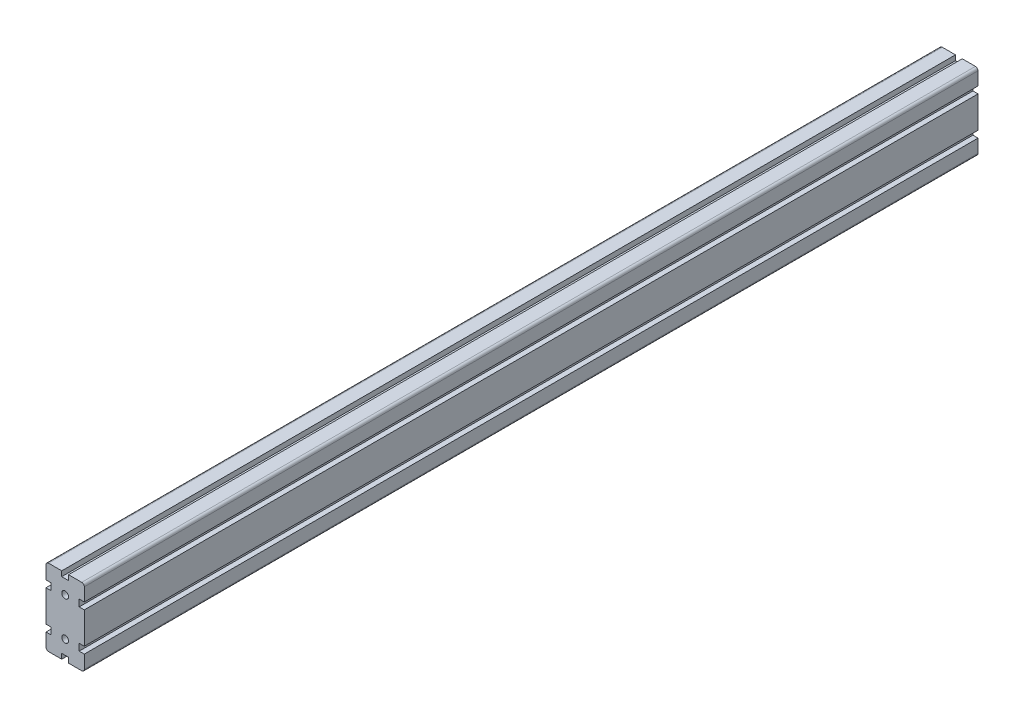
SolidWorks part; units mm, degrees
material "Zinc AC41A Alloy, As Cast"
ref_plane "Plan de face" through (0, 0, 0) normal (0, 0, 1) x (1, 0, 0)
ref_plane "Plan de dessus" through (0, 0, 0) normal (0, 1, 0) x (1, 0, 0)
ref_plane "Plan de droite" through (0, 0, 0) normal (1, 0, 0) x (0, 0, -1)
ref_plane "Plan1" through (0, 0, -1000) normal (0, 0, -1) x (-1, 0, 0)
sketch "Esquisse1" plane through (0, 0, -1000) normal (0, 0, -1) x (-1, 0, 0)
  line L0 (16.5, 26.5) -> (22.5, 26.5)
  line L1 (22.5, 26.5) -> (22.5, 42)
  line L2 (19.5, 45) -> (4, 45)
  line L3 (4, 45) -> (4, 39)
  line L4 (0, 22.5) -> (0, -22.5) construction
  line L5 (0, 22.5) -> (13.1479, 22.5) construction
  line L6 (0, -22.5) -> (12.9679, -22.5) construction
  line L7 (-4, 39) -> (-4, 45)
  line L8 (-4, 45) -> (-19.5, 45)
  line L9 (-22.5, 42) -> (-22.5, 26.5)
  line L10 (-22.5, 26.5) -> (-16.5, 26.5)
  line L11 (-16.5, 18.5) -> (-22.5, 18.5)
  line L12 (-22.5, 18.5) -> (-22.5, -18.5)
  line L13 (-4, -39) -> (4, -39)
  line L14 (16.5, -18.5) -> (16.5, -26.5)
  line L15 (-16.5, -18.5) -> (-16.5, -26.5)
  line L16 (16.5, 26.5) -> (16.5, 18.5)
  line L17 (-22.5, -18.5) -> (-16.5, -18.5)
  line L18 (-16.5, -26.5) -> (-22.5, -26.5)
  line L19 (-22.5, -26.5) -> (-22.5, -42)
  line L20 (-19.5, -45) -> (-4, -45)
  line L21 (-4, -45) -> (-4, -39)
  line L22 (4, -39) -> (4, -45)
  line L23 (4, -45) -> (19.5, -45)
  line L24 (22.5, -42) -> (22.5, -26.5)
  line L25 (22.5, -26.5) -> (16.5, -26.5)
  line L26 (16.5, -18.5) -> (22.5, -18.5)
  line L27 (-16.5, 26.5) -> (-16.5, 18.5)
  line L28 (-4, 39) -> (4, 39)
  line L29 (22.5, -18.5) -> (22.5, 18.5)
  line L30 (22.5, 18.5) -> (16.5, 18.5)
  arc A0 (22.5, 42) -> (19.5, 45) centre (19.5, 42) ccw
  arc A1 (-19.5, 45) -> (-22.5, 42) centre (-19.5, 42) ccw
  arc A2 (-22.5, -42) -> (-19.5, -45) centre (-19.5, -42) ccw
  arc A3 (19.5, -45) -> (22.5, -42) centre (19.5, -42) ccw
  circle A4 centre (0, 22.5) radius 4
  circle A5 centre (0, -22.5) radius 4
  dimension "D3" = 8
  dimension "D4" = 8
  dimension "D1" = 4
  dimension "D2" = 4
  dimension "D5" = 45
  dimension "D6" = 22.5
  dimension "D7" = 22.5
  dimension "D8" = 22.5
  dimension "D9" = 90
  dimension "D10" = 45
extrude "Boss.-Extru.1" add sketch "Esquisse1" against normal blind 1050
ref_plane "Plane1" through (0, 0, -475) normal (0, 0, -1) x (-1, 0, 0)
